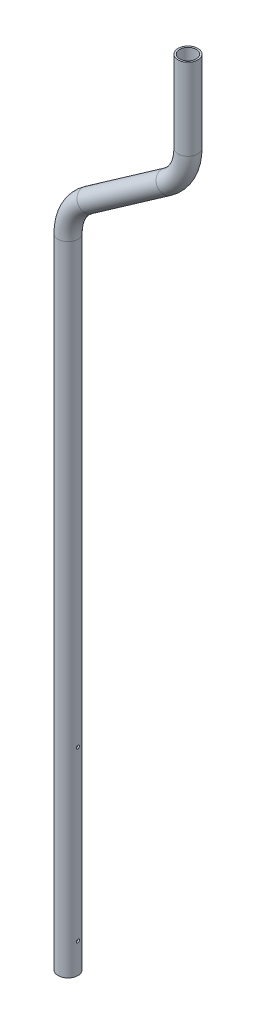
SolidWorks part; units mm, degrees
material "Plain Carbon Steel"
ref_plane "Front Plane" through (0, 0, 0) normal (0, 0, 1) x (1, 0, 0)
ref_plane "Top Plane" through (0, 0, 0) normal (0, 1, 0) x (1, 0, 0)
ref_plane "Right Plane" through (0, 0, 0) normal (1, 0, 0) x (0, 0, -1)
sketch "Sketch2" plane through (0, 0, 0) normal (0, 0, 1) x (1, 0, 0)
  line L1 (55, 0) -> (-55, 0) construction
  line L2 (0, 0) -> (0, 1350.4077)
  line L3 (0, -55) -> (0, 55) construction
  line L4 (43.3246, 1433.6335) -> (210.6754, 1550.8138)
  line L5 (254, 1634.0396) -> (254, 1806.575)
  arc A0 (210.6754, 1550.8138) -> (254, 1634.0396) centre (152.4, 1634.0396) ccw
  arc A1 (0, 1350.4077) -> (43.3246, 1433.6335) centre (101.6, 1350.4077) cw
  point P13 (254, 1581.15)
  point P16 (0, 1403.2973)
  point P19 (0, 0)
  dimension "D6" = 101.6
  dimension "D2" = 225.425
  dimension "D3" = 125
  dimension "D4" = 254
  dimension "D5" = 1806.575
ref_plane "Plane1" through (0, 1806.575, 0) normal (0, 1, 0) x (1, 0, 0)
sketch "Sketch3" plane through (0, 1806.575, 0) normal (0, 1, 0) x (1, 0, 0)
  line L0 (-55, 0) -> (55, 0) construction
  line L1 (0, -55) -> (0, 55) construction
  circle A0 centre (254, 0) radius 21.082
  circle A1 centre (254, 0) radius 17.526
  dimension "D2" = 42.164
  dimension "D3" = 35.052
  dimension "D1" = 254
sweep "Sweep1" add profiles "Sketch3" path "Sketch2"
sketch "Sketch5" plane through (0, 0, 0) normal (1, 0, 0) x (0, 0, -1)
  line L0 (-21.082, 0) -> (21.082, 0) construction
  line L2 (21.082, 0) -> (21.082, 1350.4077) construction
  circle A6 centre (0, 63.5) radius 3.3734
  circle A7 centre (0, 419.1) radius 3.3734
  dimension "D1" = 6.7469
  dimension "D4" = 21.082
  dimension "D2" = 63.5
  dimension "D3" = 355.6
extrude "Cut-Extrude1" cut sketch "Sketch5" against normal through all and the other way through all
